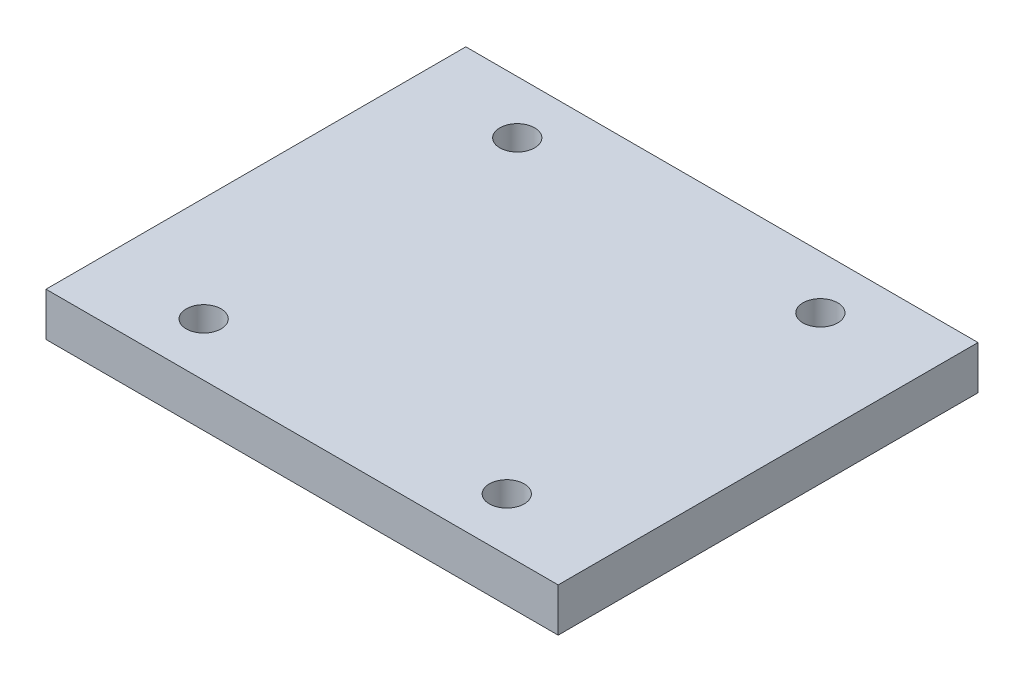
SolidWorks part; units mm, degrees
ref_plane "Front Plane" through (0, 0, 0) normal (0, 0, 1) x (1, 0, 0)
ref_plane "Top Plane" through (0, 0, 0) normal (0, 1, 0) x (1, 0, 0)
ref_plane "Right Plane" through (0, 0, 0) normal (1, 0, 0) x (0, 0, -1)
sketch "Sketch1" plane through (0, 0, 0) normal (0, 1, 0) x (1, 0, 0)
  line L1 (-15.5, -12) -> (13.9, -12)
  line L2 (-15.5, -12) -> (-15.5, 11.1)
  line L3 (-15.5, 11.1) -> (13.9, 11.1)
  line L4 (13.9, -12) -> (13.9, 11.1)
  circle A0 centre (-9.5, 8.55) radius 1
  circle A1 centre (7.9, 8.55) radius 1
  circle A2 centre (7.9, -9.45) radius 1
  circle A3 centre (-9.5, -9.45) radius 1
  point P0 (0, 0)
  dimension "D3" = 2
  dimension "D4" = 2
  dimension "D5" = 2
  dimension "D6" = 2
  dimension "D1" = 23.1
  dimension "D2" = 29.4
  dimension "D7" = 6
  dimension "D8" = 6
  dimension "D9" = 6
  dimension "D10" = 6
  dimension "D11" = 2.55
  dimension "D12" = 2.55
  dimension "D13" = 2.55
  dimension "D14" = 2.55
extrude "Boss-Extrude1" add sketch "Sketch1" along normal blind 2.5
sketch "Sketch2" plane through (0, 0, -11.1) normal (0, 0, -1) x (-1, 0, 0)
  line L4 (-13.9, 0) -> (15.5, 0)
  line L5 (15.5, 0) -> (15.5, 2.5)
  line L6 (15.5, 2.5) -> (-13.9, 2.5)
  line L7 (-13.9, 2.5) -> (-13.9, 0)
  line L8 (-13.9, 0) -> (15.5, 0)
  line L9 (15.5, 0) -> (15.5, 2.5)
  line L10 (15.5, 2.5) -> (-13.9, 2.5)
  line L11 (-13.9, 2.5) -> (-13.9, 0)
  dimension "D1" = 0
extrude "Boss-Extrude2" add sketch "Sketch2" along normal blind 0.5
sketch "Sketch3" plane through (0, 0, 12) normal (0, 0, 1) x (1, 0, 0)
  line L4 (-15.5, 0) -> (13.9, 0)
  line L5 (13.9, 0) -> (13.9, 2.5)
  line L6 (13.9, 2.5) -> (-15.5, 2.5)
  line L7 (-15.5, 2.5) -> (-15.5, 0)
  line L8 (-15.5, 0) -> (13.9, 0)
  line L9 (13.9, 0) -> (13.9, 2.5)
  line L10 (13.9, 2.5) -> (-15.5, 2.5)
  line L11 (-15.5, 2.5) -> (-15.5, 0)
  dimension "D1" = 0
extrude "Boss-Extrude3" add sketch "Sketch3" along normal blind 0.5
